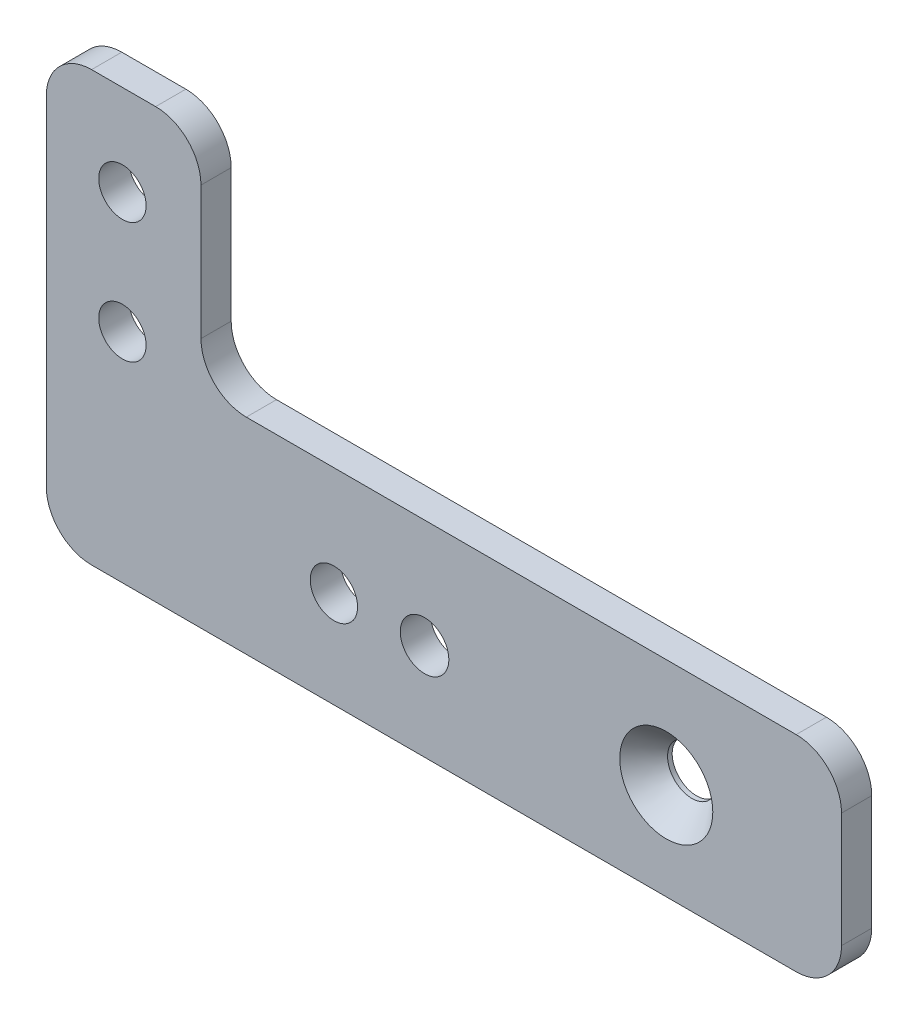
SolidWorks part; units mm, degrees
material "6061-T6 (SS)"
ref_plane "Front Plane" through (0, 0, 0) normal (0, 0, 1) x (1, 0, 0)
ref_plane "Top Plane" through (0, 0, 0) normal (0, 1, 0) x (1, 0, 0)
ref_plane "Right Plane" through (0, 0, 0) normal (1, 0, 0) x (0, 0, -1)
sketch "Sketch1" plane through (0, 0, 0) normal (0, 0, 1) x (1, 0, 0)
  line L0 (-21.59, 23.8125) -> (-37.846, 23.8125) construction
  line L1 (-45.72, -23.8125) -> (45.72, -23.8125)
  line L2 (-45.72, -23.8125) -> (-45.72, 23.8125)
  line L3 (-45.72, 23.8125) -> (45.72, 23.8125)
  line L4 (45.72, -23.8125) -> (45.72, 23.8125)
  line L5 (-45.72, -23.8125) -> (45.72, 23.8125) construction
  line L6 (-45.72, 23.8125) -> (45.72, -23.8125) construction
  line L7 (45.72, 23.8125) -> (-21.59, 23.8125)
  line L8 (45.72, 23.8125) -> (45.72, 0.3175)
  line L9 (45.72, 0.3175) -> (-21.59, 0.3175)
  line L10 (-21.59, 23.8125) -> (-21.59, 0.3175)
  line L11 (-45.72, -23.8125) -> (-37.846, -23.8125)
  line L12 (-45.72, -23.8125) -> (-45.72, 23.8125)
  line L13 (-45.72, 23.8125) -> (-37.846, 23.8125)
  line L14 (-37.846, -23.8125) -> (-37.846, 23.8125)
  line L15 (-37.846, -23.8125) -> (45.72, -23.8125)
  line L16 (-37.846, -23.8125) -> (-37.846, -21.2725)
  line L17 (-37.846, -21.2725) -> (45.72, -21.2725)
  line L18 (45.72, -23.8125) -> (45.72, -21.2725)
  line L19 (-21.59, 23.8125) -> (-37.846, 23.8125) construction
  line L20 (-29.845, 23.8125) -> (-29.845, -21.2725) construction
  circle A0 centre (-29.845, -11.1125) radius 2.4892
  circle A1 centre (-29.845, 1.5875) radius 2.4892
  circle A2 centre (-29.845, 14.2875) radius 2.4892
  circle A4 centre (-7.62, -11.1125) radius 2.4892
  circle A5 centre (1.905, -11.1125) radius 2.5527
  circle A7 centre (27.305, -11.1125) radius 2.5527
  point P0 (0, 0)
  dimension "D7" = 22.225
  dimension "D18" = 5.1054
  dimension "D19" = 4.9784
  dimension "D13" = 25.4
  dimension "D8" = 47.625
  dimension "D1" = 91.44
  dimension "D2" = 9.525
  dimension "D3" = 24.13
  dimension "D4" = 24.13
  dimension "D5" = 7.874
  dimension "D6" = 47.625
  dimension "D9" = 12.7
  dimension "D10" = 12.7
  dimension "D11" = 12.7
  dimension "D12" = 15.875
  dimension "D16" = 2.54
extrude "Boss-Extrude1" add sketch "Sketch1" along normal blind 3.175
fillet "Fillet1" radius 4.7625 6 edges at (-37.846, 23.8125, 1.5875) (-21.59, 23.8125, 1.5875) (-21.59, 0.3175, 1.5875) (45.72, 0.3175, 1.5875) (45.72, -21.2725, 1.5875) (-37.846, -21.2725, 1.5875)
hole_wizard "CSK for #10 Flat Head Machine Screw1" positions "Sketch3" profile "Sketch4" countersink size "#10" standard "ANSI Inch"
sketch "Sketch3" plane through (0, 0, 3.175) normal (0, 0, 1) x (1, 0, 0)
  point P0 (27.305, -11.1125)
sketch "Sketch4" plane through (27.305, -11.1125, 3.175) normal (1, 0, 0) x (0, -1, 0)
  line L0 (0, 0) -> (0, 20.5838)
  line L1 (0, 20.5838) -> (2.5527, 19.05)
  line L2 (2.5527, 19.05) -> (2.5527, 2.6882)
  line L3 (2.5527, 2.6882) -> (4.8895, 0)
  line L5 (4.8895, 0) -> (0, 0)
  line L6 (-2.5527, 2.6882) -> (-4.8895, 0) construction
  line L10 (0, 20.5838) -> (-2.5527, 19.05) construction
  line L11 (0, -6.35) -> (0, 107.95) construction
  dimension "Hole Dia." = 5.1054
  dimension "Hole Depth" = 19.05
  dimension "Near C'Sink Dia." = 9.779
  dimension "Near C'Sink Angle" = 82
  dimension "Drill Angle" = 118
